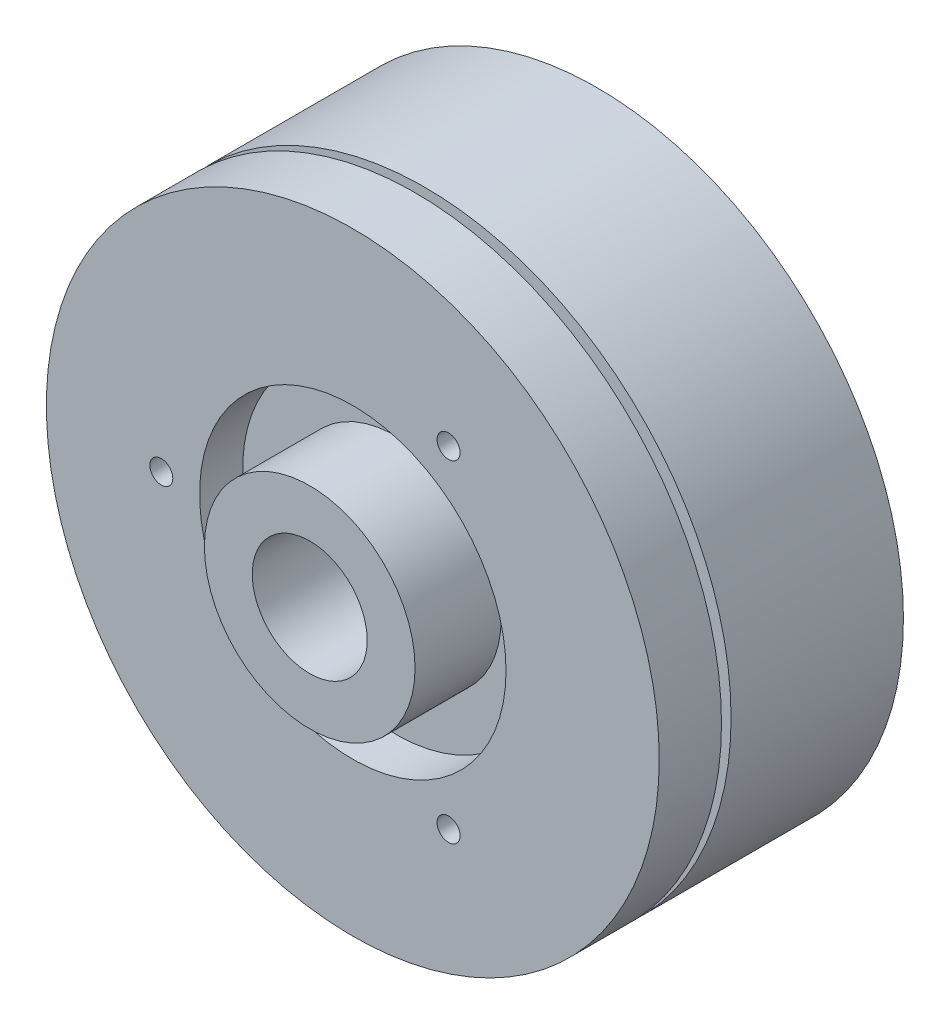
SolidWorks part; units mm, degrees
ref_plane "前视基准面" through (0, 0, 0) normal (0, 0, 1) x (1, 0, 0)
ref_plane "上视基准面" through (0, 0, 0) normal (0, 1, 0) x (1, 0, 0)
ref_plane "右视基准面" through (0, 0, 0) normal (1, 0, 0) x (0, 0, -1)
sketch "草图1" plane through (0, 0, 0) normal (0, 0, 1) x (1, 0, 0)
  circle A0 centre (0, 0) radius 16
extrude "凸台-拉伸1" add sketch "草图1" along normal blind 9
sketch "草图2" plane through (0, 0, 9) normal (0, 0, 1) x (1, 0, 0)
  circle A0 centre (0, 0) radius 6
extrude "凸台-拉伸2" add sketch "草图2" along normal blind 0.5
sketch "草图3" plane through (0, 0, 9.5) normal (0, 0, 1) x (1, 0, 0)
  circle A0 centre (0, 0) radius 16
extrude "凸台-拉伸3" add sketch "草图3" along normal blind 3.25
sketch "草图4" plane through (0, 0, 12.75) normal (0, 0, 1) x (1, 0, 0)
  circle A0 centre (0, 0) radius 5.5
extrude "凸台-拉伸4" add sketch "草图4" along normal blind 2.25
sketch "草图5" plane through (0, 0, 15) normal (0, 0, 1) x (1, 0, 0)
  circle A0 centre (0, 0) radius 3
extrude "切除-拉伸1" cut sketch "草图5" against normal blind 26.25
sketch "草图6" plane through (0, 0, 12.75) normal (0, 0, 1) x (1, 0, 0)
  circle A0 centre (0, 0) radius 5.5
  circle A1 centre (0, 0) radius 8
extrude "切除-拉伸2" cut sketch "草图6" against normal blind 2.25
sketch "草图7" plane through (0, 0, 0) normal (0, 0, -1) x (-1, 0, 0)
  circle A1 centre (8.6603, 5) radius 0.6
  circle A2 centre (-8.6603, 5) radius 0.6
  circle A3 centre (0, -10) radius 0.6
extrude "切除-拉伸3" cut sketch "草图7" against normal blind 6
sketch "草图8" plane through (0, 0, 12.75) normal (0, 0, 1) x (1, 0, 0)
  circle A2 centre (5, -8.6603) radius 0.6
  circle A3 centre (5, 8.6603) radius 0.6
  circle A4 centre (-10, 0) radius 0.6
extrude "切除-拉伸4" cut sketch "草图8" against normal blind 3
